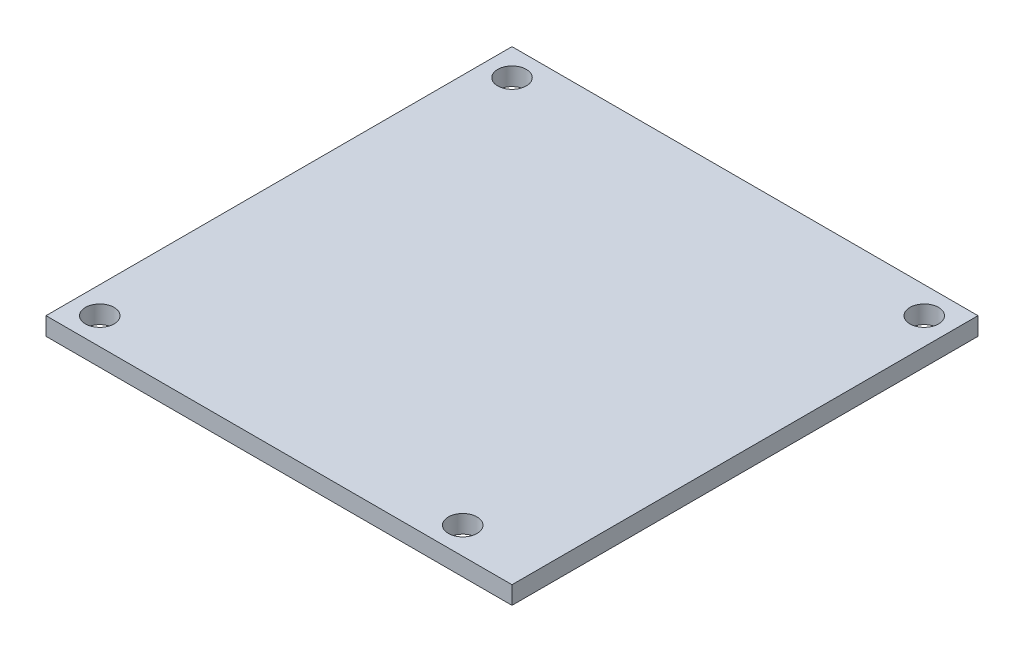
SolidWorks part; units mm, degrees
ref_plane "Front Plane" through (0, 0, 0) normal (0, 0, 1) x (1, 0, 0)
ref_plane "Top Plane" through (0, 0, 0) normal (0, 1, 0) x (1, 0, 0)
ref_plane "Right Plane" through (0, 0, 0) normal (1, 0, 0) x (0, 0, -1)
sketch "Sketch1" plane through (0, 0, 0) normal (0, 1, 0) x (1, 0, 0)
  line L1 (-26, 26) -> (26, 26)
  line L2 (-26, 26) -> (-26, -26)
  line L3 (-26, -26) -> (26, -26)
  line L4 (26, 26) -> (26, -26)
  line L5 (-26, 26) -> (26, -26) construction
  line L6 (-26, -26) -> (26, 26) construction
  point P0 (0, 0)
  dimension "D1" = 52
  dimension "D2" = 52
extrude "Extrude1" add sketch "Sketch1" along normal blind 2
sketch "Sketch2" plane through (0, 2, 0) normal (0, 1, 0) x (1, 0, 0)
  line L0 (26, 26) -> (-26, 26) construction
  line L1 (-26, 26) -> (-26, -26) construction
  line L2 (26, -26) -> (26, 26) construction
  line L3 (-26, -26) -> (26, -26) construction
  circle A0 centre (23, 23) radius 1.6
  circle A1 centre (-23, 23) radius 1.6
  circle A2 centre (-23, -23) radius 1.6
  circle A3 centre (17.5, -23) radius 1.6
  point P16 (0, 0)
  dimension "D1" = 3
  dimension "D2" = 3
  dimension "D3" = 40.5
  dimension "D4" = 3
  dimension "D6" = 3
  dimension "D9" = 3.2
extrude "Extrude2" cut sketch "Sketch2" against normal blind 2
